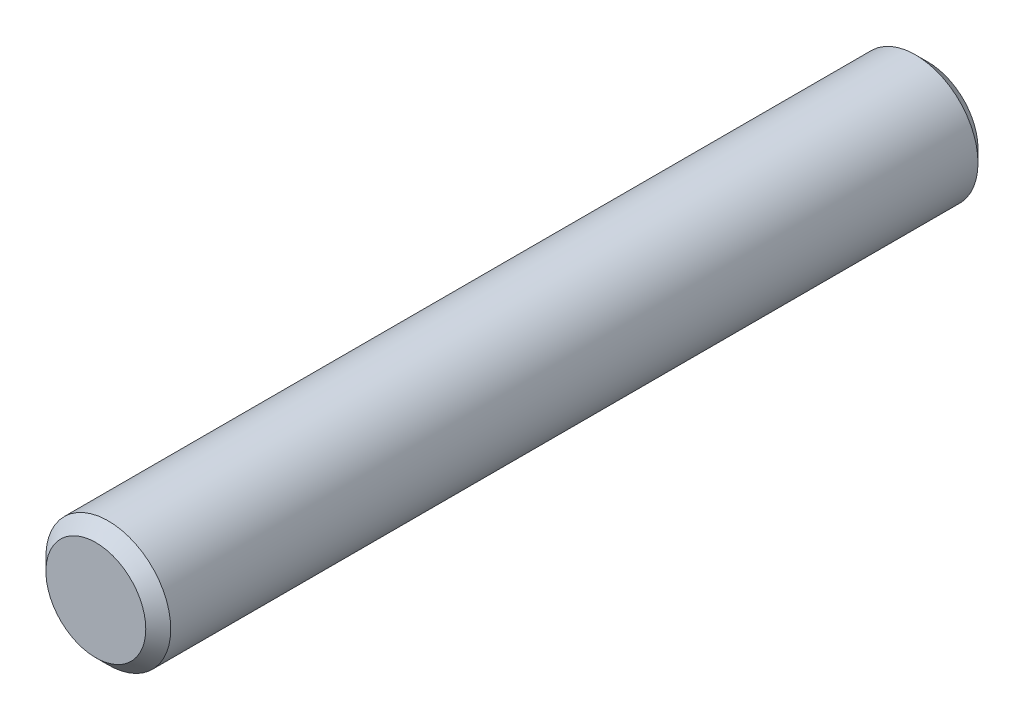
SolidWorks part; units mm, degrees
ref_plane "Front Plane" through (0, 0, 0) normal (0, 0, 1) x (1, 0, 0)
ref_plane "Top Plane" through (0, 0, 0) normal (0, 1, 0) x (1, 0, 0)
ref_plane "Right Plane" through (0, 0, 0) normal (1, 0, 0) x (0, 0, -1)
sketch "Sketch1" plane through (0, 0, 0) normal (0, 0, 1) x (1, 0, 0)
  circle A0 centre (0, 0) radius 1.5
  dimension "D1" = 3
extrude "Boss-Extrude1" add sketch "Sketch1" along normal mid plane 20
chamfer "Chamfer1" distance 0.3 angle 45 2 edges at (1.5, 0, -10) (1.5, 0, 10)
